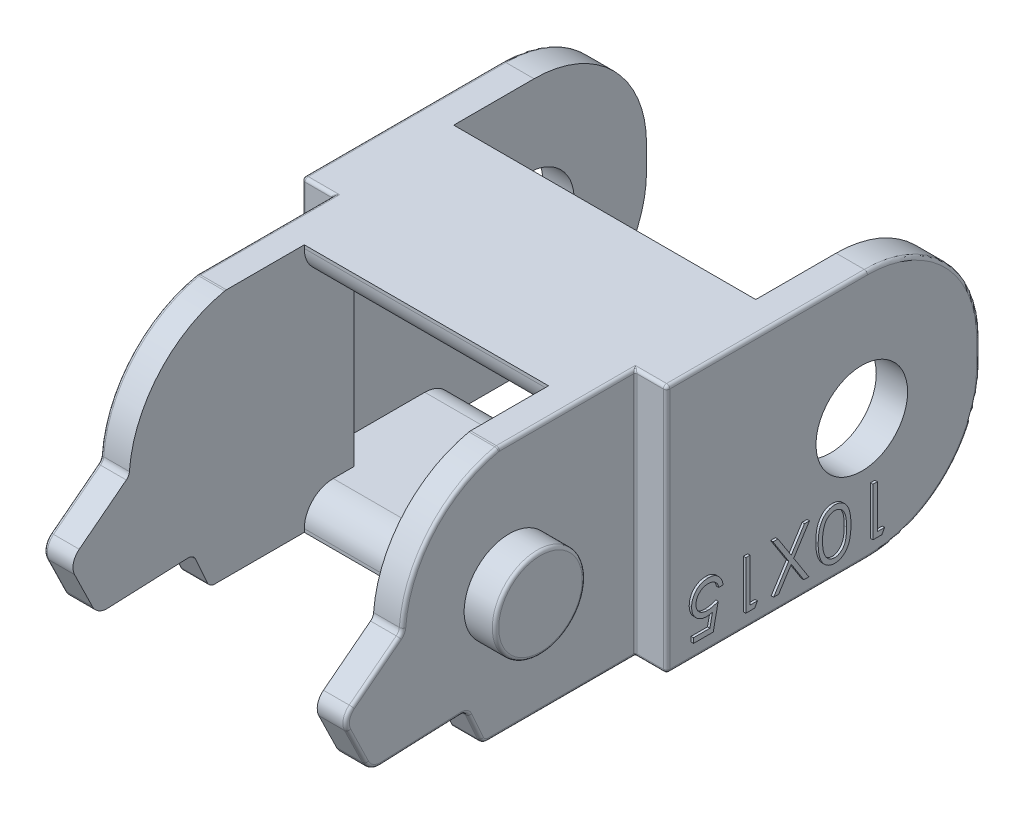
SolidWorks part; units mm, degrees
material "ABS"
ref_plane "Front Plane" through (0, 0, 0) normal (0, 0, 1) x (1, 0, 0)
ref_plane "Top Plane" through (0, 0, 0) normal (0, 1, 0) x (1, 0, 0)
ref_plane "Right Plane" through (0, 0, 0) normal (1, 0, 0) x (0, 0, -1)
sketch "Sketch1" plane through (0, 0, 0) normal (1, 0, 0) x (0, 0, -1)
  line L0 (0, 0) -> (2.85, 0) construction
  line L1 (7.35, 7.75) -> (7.35, -7.75)
  line L2 (7.35, 7.75) -> (-30.65, 7.75)
  line L3 (7.35, -7.75) -> (-30.65, -7.75)
  line L4 (2.85, 0) -> (7.35, 0) construction
  line L5 (0, 0) -> (-2.85, 0) construction
  line L6 (-20, 0) -> (-30.65, 0) construction
  line L7 (-30.65, 7.75) -> (-30.65, -7.75)
  line L8 (-2.85, 0) -> (-12.15, 0) construction
  line L9 (-12.15, 0) -> (-20, 0) construction
  line L10 (-12.15, 7.75) -> (-12.15, -7.75) construction
  circle A0 centre (0, 0) radius 2.85
  circle A1 centre (-20, 0) radius 2.8 construction
  dimension "D1" = 5.7
  dimension "D6" = 5.6
  dimension "D2" = 4.5
  dimension "D3" = 15.5
  dimension "D4" = 20
  dimension "D5" = 38
  dimension "D7" = 19.5
extrude "Boss-Extrude1" add sketch "Sketch1" along normal mid plane 22.7
fillet "Fillet1" radius 7 2 edges at (0, -7.75, -7.35) (0, 7.75, -7.35)
sketch "Sketch2" plane through (0, 0, 0) normal (1, 0, 0) x (0, 0, -1)
  line L0 (0, 0) -> (7.35, 0) construction
  line L1 (7.35, -0.75) -> (7.35, 0.75) construction
  line L2 (7.35, 0) -> (7.35, 7.75) construction
  line L3 (7.35, 7.75) -> (-20.65, 7.75) construction
  line L4 (0.35, 7.75) -> (-30.65, 7.75) construction
  line L5 (-20.65, 7.75) -> (-20.65, 0.75) construction
  line L6 (-20.65, 0.75) -> (-26.65, 0.75) construction
  line L7 (-26.65, 0.75) -> (-30.4, -2.1531)
  line L8 (-30.4, -2.1531) -> (-28.65, -5.75)
  line L9 (-30.65, -7.75) -> (0.35, -7.75) construction
  line L10 (-28.65, -5.75) -> (-22.6552, -5.5)
  line L11 (-22.6552, -5.5) -> (-21.65, -7.75)
  line L12 (-20.65, 7.75) -> (-30.65, 7.75)
  line L13 (-30.65, 7.75) -> (-30.65, -7.75) construction
  line L14 (-30.65, 7.75) -> (-30.65, -7.75) construction
  line L15 (-30.65, -7.75) -> (-21.65, -7.75)
  line L16 (-30.65, 7.75) -> (-37.65, 7.75)
  line L17 (-37.65, 7.75) -> (-37.65, -7.75)
  line L18 (-37.65, -7.75) -> (-30.65, -7.75)
  arc A0 (-20.65, 7.75) -> (-26.65, 0.75) centre (-19.1582, 0.3999) ccw
  dimension "D8" = 7.5
  dimension "D1" = 28
  dimension "D2" = 34
  dimension "D3" = 7
  dimension "D4" = 36
  dimension "D5" = 37.75
  dimension "D6" = 4
  dimension "D7" = 2
  dimension "D9" = 6
  dimension "D10" = 2.25
  dimension "D11" = 29
  dimension "D12" = 45
  dimension "D13" = 6
  dimension "D14" = 3.75
  dimension "D15" = 8.75
  dimension "D16" = 2.4643
extrude "Cut-Extrude1" cut sketch "Sketch2" against normal mid plane 22.7
fillet "Fillet2" radius 1 2 edges at (0, -2.1531, 30.4) (0, -5.75, 28.65)
fillet "Fillet3" radius 0.5 4 edges at (0, 7.75, 20.65) (0, 0.75, 26.65) (0, -5.5, 22.6552) (0, -7.75, 21.65)
sketch "Sketch4" plane through (11.35, 0, 0) normal (1, 0, 0) x (0, 0, -1)
  line L0 (-12.15, 7.75) -> (-12.15, -7.75) construction
  line L1 (-12.15, 7.75) -> (-12.15, -7.75)
  line L7 (0.35, 7.75) -> (-20.5989, 7.75)
  line L8 (-26.829, 0.6114) -> (-29.7574, -1.6556)
  line L9 (-30.0445, -2.8839) -> (-28.9365, -5.1611)
  line L10 (-27.9956, -5.7227) -> (-22.9942, -5.5141)
  line L11 (-22.5168, -5.8097) -> (-21.7823, -7.454)
  line L12 (-21.3258, -7.75) -> (0.35, -7.75)
  line L13 (7.35, -0.75) -> (7.35, 0.75)
  line L14 (-12.15, 7.75) -> (-20.5989, 7.75)
  line L15 (-26.829, 0.6114) -> (-29.7574, -1.6556)
  line L16 (-30.0445, -2.8839) -> (-28.9365, -5.1611)
  line L17 (-27.9956, -5.7227) -> (-22.9942, -5.5141)
  line L18 (-22.5168, -5.8097) -> (-21.7823, -7.454)
  line L19 (-21.3258, -7.75) -> (-12.15, -7.75)
  circle A0 centre (-20, 0) radius 2.8 construction
  circle A1 centre (-20, 0) radius 2.8
  arc A9 (-20.5989, 7.75) -> (-20.7018, 7.7393) centre (-20.5989, 7.25) ccw
  arc A10 (-20.7018, 7.7393) -> (-26.6366, 0.9688) centre (-19.1582, 0.3999) ccw
  arc A11 (-26.829, 0.6114) -> (-26.6366, 0.9688) centre (-27.1351, 1.0068) ccw
  arc A12 (-29.7574, -1.6556) -> (-30.0445, -2.8839) centre (-29.1452, -2.4464) ccw
  arc A13 (-28.9365, -5.1611) -> (-27.9956, -5.7227) centre (-28.0373, -4.7236) ccw
  arc A14 (-22.5168, -5.8097) -> (-22.9942, -5.5141) centre (-22.9733, -6.0137) ccw
  arc A15 (-21.7823, -7.454) -> (-21.3258, -7.75) centre (-21.3258, -7.25) ccw
  arc A16 (0.35, -7.75) -> (7.35, -0.75) centre (0.35, -0.75) ccw
  arc A17 (7.35, 0.75) -> (0.35, 7.75) centre (0.35, 0.75) ccw
  arc A18 (-20.5989, 7.75) -> (-20.7018, 7.7393) centre (-20.5989, 7.25) ccw
  arc A19 (-20.7018, 7.7393) -> (-26.6366, 0.9688) centre (-19.1582, 0.3999) ccw
  arc A20 (-26.829, 0.6114) -> (-26.6366, 0.9688) centre (-27.1351, 1.0068) ccw
  arc A21 (-29.7574, -1.6556) -> (-30.0445, -2.8839) centre (-29.1452, -2.4464) ccw
  arc A22 (-28.9365, -5.1611) -> (-27.9956, -5.7227) centre (-28.0373, -4.7236) ccw
  arc A23 (-22.5168, -5.8097) -> (-22.9942, -5.5141) centre (-22.9733, -6.0137) ccw
  arc A24 (-21.7823, -7.454) -> (-21.3258, -7.75) centre (-21.3258, -7.25) ccw
  dimension "D1" = 0
extrude "Cut-Extrude2" cut sketch "Sketch4" against normal blind 1.95
mirror "Mirror1" about plane through (0, 0, 0) normal (1, 0, 0) of "Cut-Extrude2"
sketch "Sketch5" plane through (0, 0, 0) normal (0, 1, 0) x (1, 0, 0)
  line L0 (0, 0) -> (0, 7.35) construction
  line L1 (-11.35, 7.35) -> (11.35, 7.35) construction
  line L3 (-9.4, 7.35) -> (9.4, 7.35)
  line L4 (-9.4, 7.35) -> (-9.4, -4.65)
  line L5 (-9.4, -4.65) -> (9.4, -4.65)
  line L6 (9.4, 7.35) -> (9.4, -4.65)
  line L7 (11.35, 0.35) -> (11.35, 7.35) construction
  line L8 (-11.35, 7.35) -> (-11.35, 0.35) construction
  line L9 (0, 0) -> (0, -4.65) construction
  line L10 (0, -4.65) -> (0, -15.75) construction
  line L11 (0, -15.75) -> (0, -30.1452) construction
  line L12 (-9.4, -30.1452) -> (9.4, -30.1452) construction
  line L14 (-7.6, -15.75) -> (7.6, -15.75)
  line L15 (-7.6, -15.75) -> (-7.6, -30.1452)
  line L16 (-7.6, -30.1452) -> (7.6, -30.1452)
  line L17 (7.6, -15.75) -> (7.6, -30.1452)
  line L18 (9.4, -26.829) -> (9.4, -29.7574) construction
  line L19 (-9.4, -26.829) -> (-9.4, -29.7574) construction
  dimension "D1" = 18.8
  dimension "D2" = 1.95
  dimension "D3" = 1.95
  dimension "D4" = 12
  dimension "D5" = 15.2
  dimension "D6" = 1.8
  dimension "D7" = 1.8
  dimension "D8" = 11.1
  dimension "D9" = 14.3952
  dimension "D10" = 23.1
extrude "Cut-Extrude3" cut sketch "Sketch5" against normal through all both and the other way through all
sketch "Sketch6" plane through (0, 0, 15.75) normal (0, 0, 1) x (1, 0, 0)
  line L0 (7.6, 7.75) -> (-7.6, 7.75) construction
  line L1 (-7.6, 5.75) -> (7.6, 5.75)
  line L2 (-7.6, 5.75) -> (-7.6, -5.75)
  line L3 (-7.6, -5.75) -> (7.6, -5.75)
  line L4 (7.6, 5.75) -> (7.6, -5.75)
  line L5 (-7.6, 5.75) -> (7.6, -5.75) construction
  line L6 (-7.6, -5.75) -> (7.6, 5.75) construction
  line L7 (7.6, -7.75) -> (7.6, 7.75) construction
  point P0 (0, 0)
  dimension "D1" = 2
  dimension "D2" = 15.2
  dimension "D3" = 11.5
extrude "Cut-Extrude4" cut sketch "Sketch6" against normal up to surface (11.1 mm away) up to face at (0, 0, 4.65)
sketch "Sketch7" plane through (0, 5.75, 0) normal (0, 1, 0) x (1, 0, 0)
  line L0 (0, 0) -> (0, 7.35) construction
  line L1 (-9.4, 7.35) -> (9.4, 7.35)
  line L2 (0, 0) -> (0, -10.9) construction
  line L3 (-9.4, -10.9) -> (9.4, -10.9) construction
  line L4 (-9.4, 7.35) -> (-9.4, -10.9)
  line L5 (9.4, -10.9) -> (9.4, 7.35)
  line L6 (-9.4, -10.9) -> (-7.6, -12.65)
  line L7 (-7.6, -4.65) -> (-7.6, -15.75) construction
  line L8 (-7.6, -12.65) -> (7.6, -12.65)
  line L9 (7.6, -4.65) -> (7.6, -15.75) construction
  line L10 (7.6, -12.65) -> (9.4, -10.9)
  dimension "D1" = 18.25
  dimension "D2" = 20
extrude "Cut-Extrude5" cut sketch "Sketch7" against normal up to surface (11.5 mm away) up to face at (0, -5.75, 10.2)
fillet "Fillet4" radius 0.2 2 edges at (-11.35, 0, 17.2) (11.35, 0, 17.2)
sketch "Sketch8" plane through (11.35, 0, 0) normal (1, 0, 0) x (0, 0, -1)
  line L0 (-12.15, -3.75) -> (1.85, -3.75) construction
  line L1 (-12.15, -7.75) -> (-12.15, 7.75) construction
  line L2 (-12.15, -7.75) -> (0.35, -7.75) construction
  text T0 "10X15" font "Century Gothic" height 3
  dimension "D1" = 14
  dimension "D2" = 4
extrude "Boss-Extrude2" add sketch "Sketch8" along normal blind 0.15
sketch "Sketch9" plane through (-11.35, 0, 0) normal (-1, 0, 0) x (0, 0, 1)
  line L0 (12.15, -3.75) -> (11.15, -3.75) construction
  line L1 (12.15, -7.75) -> (12.15, 7.75) construction
  line L2 (11.15, -3.75) -> (-2.85, -3.75) construction
  line L3 (12.15, -7.75) -> (-0.35, -7.75) construction
  text T0 "10X15" font "Century Gothic" height 3
  dimension "D1" = 4
  dimension "D2" = 1
  dimension "D3" = 14
extrude "Boss-Extrude3" add sketch "Sketch9" along normal blind 0.15
fillet "Fillet5" radius 1.8 4 edges at (0, 5.75, 4.65) (0, -5.75, 4.65) (0, -5.75, 15.75) (0, 5.75, 15.75)
fillet "Fillet6" radius 0.2 36 edges at (-11.35, -7.75, 5.9) (-11.35, -5.6997, -5.2997) (-11.35, 0, -7.35) (-11.35, 5.6997, -5.2997) (11.35, -7.75, 5.9) (11.35, -5.6997, -5.2997) (11.35, 0, -7.35) (11.35, 5.6997, -5.2997) (-9.4, -7.75, 16.7379) (-9.4, -7.6695, 21.5978) (-9.4, -6.6319, 22.1495) (-9.4, -5.5886, 22.7101) (-9.4, -5.6184, 25.4949) (-9.4, -5.5822, 28.5499) (-9.4, -4.0225, 29.4905) (-9.4, -2.2188, 30.119) (-9.4, -0.5221, 28.2932) (-9.4, 0.7697, 26.6949) (-9.4, 5.3437, 24.7981) (-9.4, 7.7473, 20.6506) (9.4, -7.75, 16.7379) (9.4, -7.6695, 21.5978) (9.4, -6.6319, 22.1495) (9.4, -5.5886, 22.7101) (9.4, -5.6184, 25.4949) (9.4, -5.5822, 28.5499) (9.4, -4.0225, 29.4905) (9.4, -2.2188, 30.119) (9.4, -0.5221, 28.2932) (9.4, 0.7697, 26.6949) (9.4, 5.3437, 24.7981) (9.4, 7.7473, 20.6506) (-11.35, 7.75, 5.9) (11.35, 7.75, 5.9) (-9.4, 7.75, 16.3744) (9.4, 7.75, 16.3744)
fillet "Fillet7" radius 0.2 10 edges at (-10.175, -7.75, 12.15) (-11.2914, -7.6914, 12.15) (-11.35, 0, 12.15) (-11.2914, 7.6914, 12.15) (10.175, -7.75, 12.15) (11.2914, -7.6914, 12.15) (11.35, 0, 12.15) (11.2914, 7.6914, 12.15) (-10.175, 7.75, 12.15) (10.175, 7.75, 12.15)
fillet "Fillet8" radius 0.1 6 edges at (-9.3414, -7.6914, 12.0914) (-9.3414, 7.6914, 12.0914) (9.3414, -7.6914, 12.0914) (9.3414, 7.6914, 12.0914) (-9.4, 0, 12.15) (9.4, 0, 12.15)
